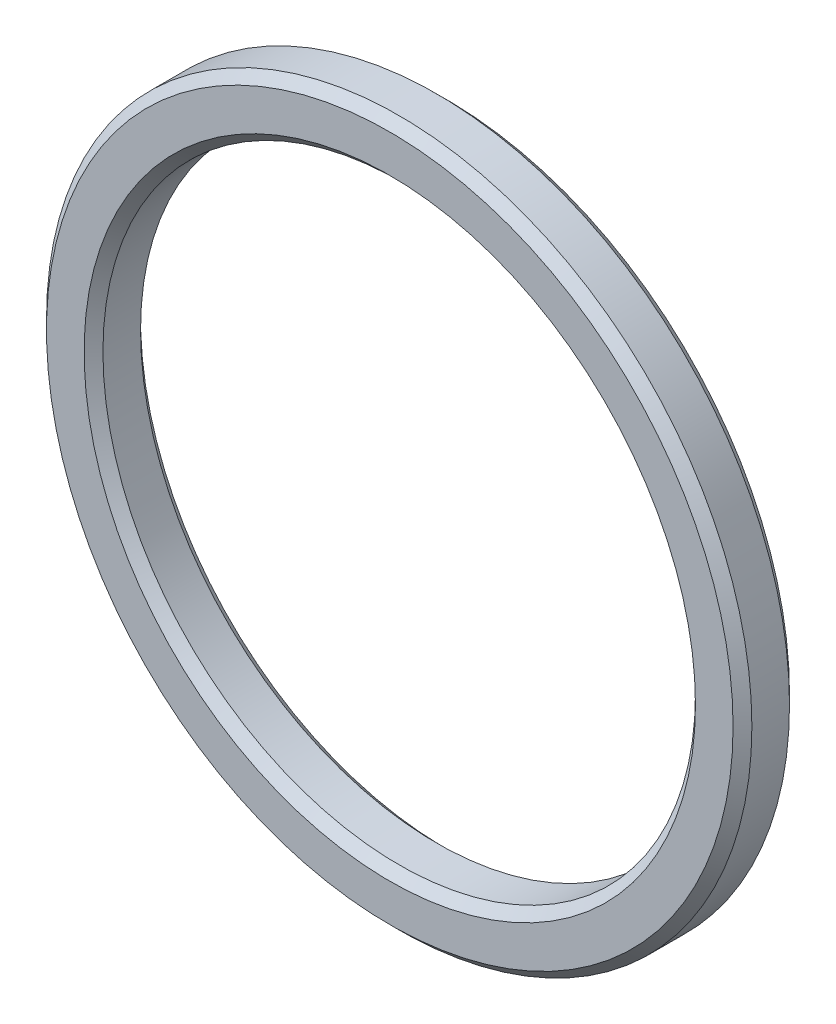
SolidWorks part; units mm, degrees
material "Polylactic Acid (PLA)"
ref_plane "Front Plane" through (0, 0, 0) normal (0, 0, 1) x (1, 0, 0)
ref_plane "Top Plane" through (0, 0, 0) normal (0, 1, 0) x (1, 0, 0)
ref_plane "Right Plane" through (0, 0, 0) normal (1, 0, 0) x (0, 0, -1)
sketch "Sketch1" plane through (0, 0, 0) normal (0, 0, 1) x (1, 0, 0)
  circle A0 centre (0, 0) radius 18.75
  circle A2 centre (0, 0) radius 15.75
  dimension "D1" = 37.5
  dimension "D2" = 3
extrude "Boss-Extrude1" add sketch "Sketch1" along normal blind 3 contours A2
chamfer "Chamfer1" distance 0.5 angle 45 4 edges at (15.75, 0, 0) (15.75, 0, 3) (18.75, 0, 0) (18.75, 0, 3)
